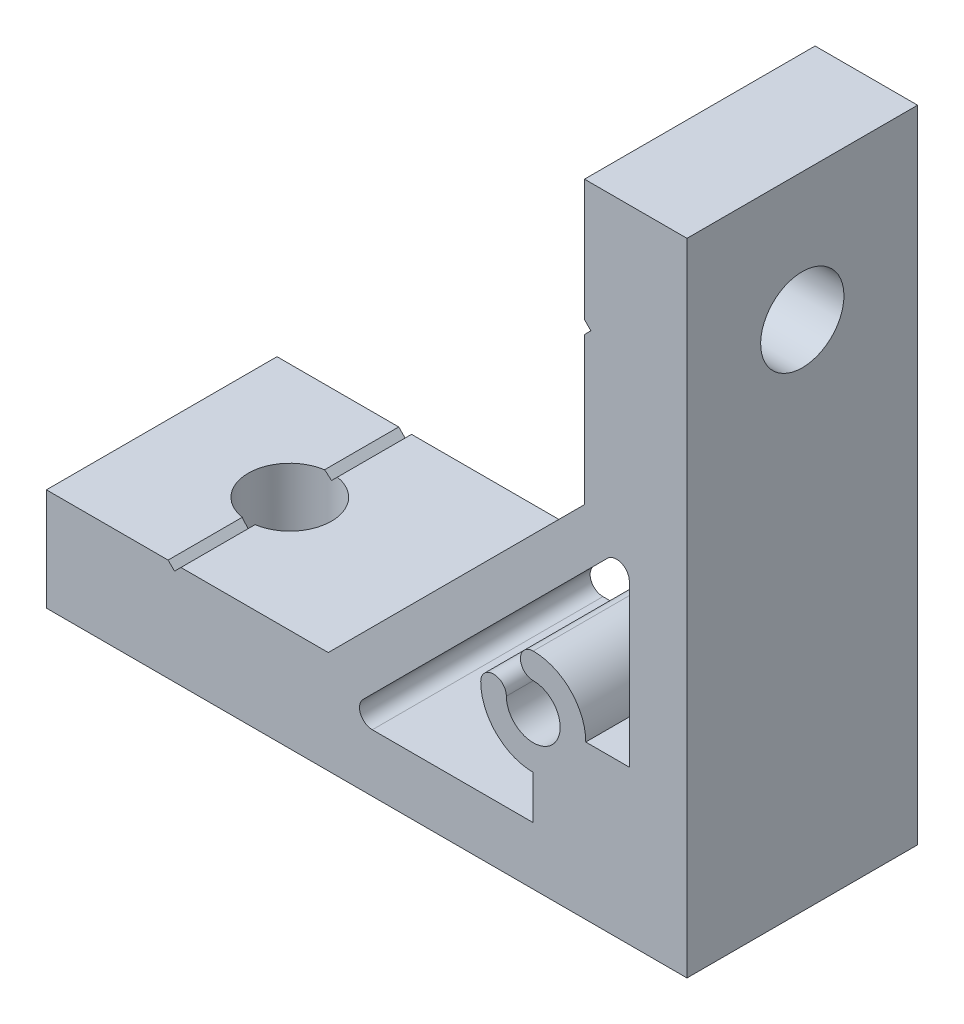
SolidWorks part; units mm, degrees
material "6063 T5"
ref_plane "Спереди" through (0, 0, 0) normal (0, 0, 1) x (1, 0, 0)
ref_plane "Сверху" through (0, 0, 0) normal (0, 1, 0) x (1, 0, 0)
ref_plane "Справа" through (0, 0, 0) normal (1, 0, 0) x (0, 0, -1)
sketch "Эскиз1" plane through (0, 0, 0) normal (0, 0, 1) x (1, 0, 0)
  line L0 (-50, 0) -> (0, 0)
  line L1 (0, 0) -> (0, 50)
  line L2 (0, 50) -> (-8, 50)
  line L3 (-8, 50) -> (-8, 40.5)
  line L4 (-8, 40.5) -> (-7.5, 40)
  line L5 (-7.5, 40) -> (-8, 39.5)
  line L6 (-8, 39.5) -> (-8, 28)
  line L7 (-8, 28) -> (-28, 8)
  line L8 (-28, 8) -> (-39.5, 8)
  line L9 (-39.5, 8) -> (-40, 7.5)
  line L10 (-40, 7.5) -> (-40.5, 8)
  line L11 (-40.5, 8) -> (-50, 8)
  line L12 (-50, 8) -> (-50, 0)
  line L13 (-4.5, 12) -> (-4.5, 24.5603)
  line L14 (-6.2071, 25.2674) -> (-25.2674, 6.2071)
  line L15 (-24.5603, 4.5) -> (-12, 4.5)
  line L16 (-12, 4.5) -> (-12, 7.9)
  line L17 (-7.9, 12) -> (-4.5, 12)
  arc A0 (-4.5, 24.5603) -> (-6.2071, 25.2674) centre (-5.5, 24.5603) ccw
  arc A1 (-25.2674, 6.2071) -> (-24.5603, 4.5) centre (-24.5603, 5.5) ccw
  arc A2 (-12, 7.9) -> (-16.1, 12) centre (-12, 12) cw
  arc A3 (-16.1, 12) -> (-14.1, 12) centre (-15.1, 12) cw
  arc A4 (-14.1, 12) -> (-12, 14.1) centre (-12, 12) ccw
  arc A5 (-12, 14.1) -> (-12, 16.1) centre (-12, 15.1) cw
  arc A6 (-12, 16.1) -> (-7.9, 12) centre (-12, 12) cw
  dimension "D6" = 4.2
  dimension "D7" = 1
  dimension "D9" = 1
  dimension "D1" = 50
  dimension "D2" = 8
  dimension "D3" = 135
  dimension "D4" = 12
  dimension "D5" = 12
  dimension "D8" = 28
  dimension "D10" = 3.2
  dimension "D11" = 4.5
  dimension "D12" = 40
  dimension "D13" = 1
extrude "Бобышка-Вытянуть1" add sketch "Эскиз1" along normal mid plane 18
sketch "Эскиз2" plane through (-8, 0, 0) normal (-1, 0, 0) x (0, 0, 1)
  line L0 (9, 40) -> (-9, 40) construction
  circle A0 centre (0, 40) radius 3.25
  dimension "D1" = 6.5
extrude "Вырез-Вытянуть1" cut sketch "Эскиз2" against normal through all
sketch "Эскиз3" plane through (0, 8, 0) normal (0, 1, 0) x (1, 0, 0)
  line L0 (-40, -9) -> (-40, 9) construction
  circle A0 centre (-40, 0) radius 3.25
  dimension "D1" = 6.5
extrude "Вырез-Вытянуть2" cut sketch "Эскиз3" against normal through all
